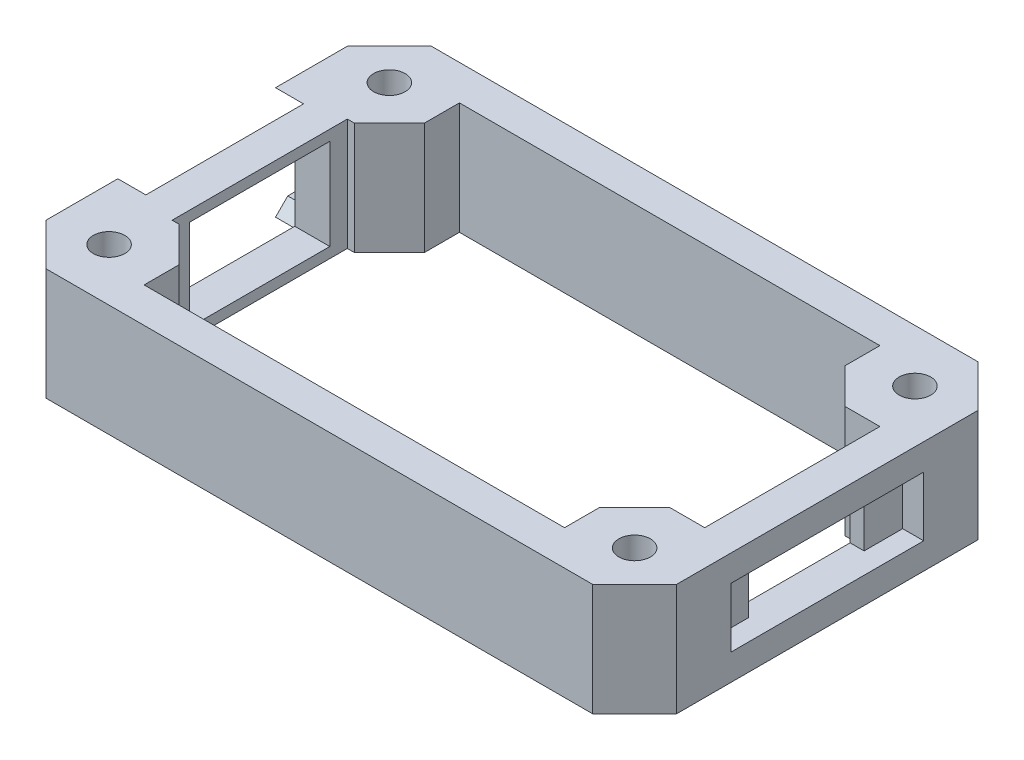
SolidWorks part; units mm, degrees
ref_plane "Front Plane" through (0, 0, 0) normal (0, 0, 1) x (1, 0, 0)
ref_plane "Top Plane" through (0, 0, 0) normal (0, 1, 0) x (1, 0, 0)
ref_plane "Right Plane" through (0, 0, 0) normal (1, 0, 0) x (0, 0, -1)
sketch "Sketch1" plane through (0, 0, 0) normal (0, 1, 0) x (1, 0, 0)
  line L1 (-45, -27.5) -> (45, -27.5)
  line L2 (-45, -27.5) -> (-45, 27.5)
  line L3 (-45, 27.5) -> (45, 27.5)
  line L4 (45, -27.5) -> (45, 27.5)
  line L5 (-45, -27.5) -> (45, 27.5) construction
  line L6 (-45, 27.5) -> (45, -27.5) construction
  point P0 (0, 0)
  dimension "D1" = 55
  dimension "D2" = 90
extrude "Boss-Extrude1" add sketch "Sketch1" along normal blind 16
sketch "Sketch2" plane through (-45, 0, 0) normal (-1, 0, 0) x (0, 0, 1)
  line L0 (-27.5, 0) -> (27.5, 0) construction
  line L1 (-17.5, 1.75) -> (17.5, 1.75)
  line L2 (-17.5, 1.75) -> (-17.5, 14.25)
  line L3 (-17.5, 14.25) -> (17.5, 14.25)
  line L4 (17.5, 1.75) -> (17.5, 14.25)
  line L5 (-17.5, 1.75) -> (17.5, 14.25) construction
  line L6 (-17.5, 14.25) -> (17.5, 1.75) construction
  line L7 (-11, -0.25) -> (11, -0.25)
  line L8 (-11, -0.25) -> (-11, 16.25)
  line L9 (-11, 16.25) -> (11, 16.25)
  line L10 (11, -0.25) -> (11, 16.25)
  line L11 (-11, -0.25) -> (11, 16.25) construction
  line L12 (-11, 16.25) -> (11, -0.25) construction
  line L13 (-27.5, 16) -> (-27.5, 0) construction
  line L14 (-11, 16.25) -> (-13, 14.25)
  line L15 (11, 16.25) -> (13, 14.25)
  line L16 (-11, -0.25) -> (-13, 1.75)
  line L17 (11, -0.25) -> (13, 1.75)
  point P0 (0, 8)
  point P5 (0, 8)
  point P14 (0, 0)
  point P17 (-27.5, 8)
  line M13 (-27.5, 0) -> (27.5, 0)
  line M15 (27.5, 16) -> (-27.5, 16)
  dimension "D1" = 22
  dimension "D2" = 12.5
  dimension "D3" = 35
  dimension "D4" = 16.5
  dimension "D5" = 45
  dimension "D6" = 45
  dimension "D7" = 45
  dimension "D8" = 45
extrude "Cut-Extrude1" cut sketch "Sketch2" against normal blind 4 contours L3 L10 L8 M15 | L15 L10 L3 M15 | L14 L3 L8 M15 | L1 L8 L3 L2 | L1 L10 L3 L8 | L10 L1 L4 L3 | L10 L1 L8 M13 | L17 L1 L10 M13 | L16 L8 L1 M13
sketch "Sketch3" plane through (-41, 0, 0) normal (-1, 0, 0) x (0, 0, 1)
  line L0 (-11, 20.75) -> (11, 20.75) construction
  line L1 (-10, 1.5) -> (10, 1.5)
  line L2 (-10, 1.5) -> (-10, 14.5)
  line L3 (-10, 14.5) -> (10, 14.5)
  line L4 (10, 1.5) -> (10, 14.5)
  line L5 (-10, 1.5) -> (10, 14.5) construction
  line L6 (-10, 14.5) -> (10, 1.5) construction
  line L7 (-17.5, 1.75) -> (-17.5, 14.25) construction
  point P0 (0, 8)
  point P7 (0, 20.75)
  point P11 (-17.5, 8)
  dimension "D1" = 20
  dimension "D2" = 13
extrude "Cut-Extrude2" cut sketch "Sketch3" against normal blind 20
chamfer "Chamfer1" distance 6 angle 45 4 edges at (45, 8, -27.5) (45, 8, 27.5) (-45, 8, 27.5) (-45, 8, -27.5)
hole_wizard "M4 Clearance Hole1" positions "Sketch5" profile "Sketch6" hole size "M4" standard "ANSI Metric" end condition through all
sketch "Sketch5" plane through (0, 16, 0) normal (0, 1, 0) x (1, 0, 0)
  line L2 (-37.5, -20) -> (37.5, -20)
  line L3 (-37.5, -20) -> (-37.5, 20)
  line L4 (-37.5, 20) -> (37.5, 20)
  line L5 (37.5, -20) -> (37.5, 20)
  line L6 (-37.5, -20) -> (37.5, 20) construction
  line L7 (-37.5, 20) -> (37.5, -20) construction
  point P3 (0, 0)
  point P4 (37.5, 20)
  point P105 (-37.5, -20)
  point P106 (-37.5, 20)
  point P107 (37.5, -20)
  dimension "D1" = 75
  dimension "D2" = 40
sketch "Sketch6" plane through (0, 16, 0) normal (1, 0, 0) x (0, 0, 1)
  line L0 (0, 0) -> (0, 16)
  line L1 (0, 16) -> (2.25, 16)
  line L2 (2.25, 16) -> (2.25, 0)
  line L5 (2.25, 0) -> (0, 0)
  line L11 (0, -6.35) -> (0, 107.95) construction
  dimension "Thru Hole Dia." = 4.5
  dimension "Thru Hole Depth" = 16
sketch "Sketch7" plane through (45, 0, 0) normal (1, 0, 0) x (0, 0, -1)
  line L0 (-21.5, 0) -> (21.5, 0) construction
  line L1 (-13.75, 3.75) -> (13.75, 3.75)
  line L2 (-13.75, 3.75) -> (-13.75, 12.25)
  line L3 (-13.75, 12.25) -> (13.75, 12.25)
  line L4 (13.75, 3.75) -> (13.75, 12.25)
  line L5 (-13.75, 3.75) -> (13.75, 12.25) construction
  line L6 (-13.75, 12.25) -> (13.75, 3.75) construction
  line L7 (-21.5, 16) -> (-21.5, 0) construction
  point P0 (0, 8)
  point P5 (0, 0)
  point P8 (0, 0)
  point P11 (-21.5, 8)
  dimension "D1" = 8.5
  dimension "D2" = 27.5
extrude "Cut-Extrude3" cut sketch "Sketch7" against normal blind 3
sketch "Sketch8" plane through (42, 0, 0) normal (1, 0, 0) x (0, 0, -1)
  line L0 (13.75, 12.25) -> (-13.75, 12.25) construction
  line L1 (-8.25, 3.75) -> (8.25, 3.75)
  line L2 (-8.25, 3.75) -> (-8.25, 12.25)
  line L3 (-8.25, 12.25) -> (8.25, 12.25)
  line L4 (8.25, 3.75) -> (8.25, 12.25)
  line L5 (-8.25, 3.75) -> (8.25, 12.25) construction
  line L6 (-8.25, 12.25) -> (8.25, 3.75) construction
  line L7 (-13.75, 3.75) -> (13.75, 3.75) construction
  point P0 (0, 8)
  point P9 (0, 0)
  point P10 (0, 3.75)
  dimension "D1" = 16.5
extrude "Cut-Extrude4" cut sketch "Sketch8" against normal blind 12
sketch "Sketch9" plane through (0, 16, 0) normal (0, 1, 0) x (1, 0, 0)
  line L24 (40, -19.4289) -> (40, 19.4289)
  line L25 (40, 19.4289) -> (36.9289, 22.5)
  line L26 (36.9289, 22.5) -> (-36.9289, 22.5)
  line L27 (-36.9289, 22.5) -> (-40, 19.4289)
  line L28 (-40, 19.4289) -> (-40, 16.25)
  line L29 (-40, 16.25) -> (-36, 16.25)
  line L30 (-36, 16.25) -> (-36, -16.25)
  line L31 (-36, -16.25) -> (-40, -16.25)
  line L32 (-40, -16.25) -> (-40, -19.4289)
  line L33 (-40, -19.4289) -> (-36.9289, -22.5)
  line L34 (-36.9289, -22.5) -> (36.9289, -22.5)
  line L35 (36.9289, -22.5) -> (40, -19.4289)
  line L36 (40, -19.4289) -> (40, 19.4289)
  line L37 (40, 19.4289) -> (36.9289, 22.5)
  line L38 (36.9289, 22.5) -> (-36.9289, 22.5)
  line L39 (-36.9289, 22.5) -> (-40, 19.4289)
  line L40 (-40, 19.4289) -> (-40, 16.25)
  line L41 (-40, 16.25) -> (-36, 16.25)
  line L42 (-36, 16.25) -> (-36, -16.25)
  line L43 (-36, -16.25) -> (-40, -16.25)
  line L44 (-40, -16.25) -> (-40, -19.4289)
  line L45 (-40, -19.4289) -> (-36.9289, -22.5)
  line L46 (-36.9289, -22.5) -> (36.9289, -22.5)
  line L47 (36.9289, -22.5) -> (40, -19.4289)
  line L79 (30, -12.5) -> (40, -12.5)
  line L80 (30, -12.5) -> (30, -22.5)
  line L81 (30, -22.5) -> (40, -22.5)
  line L82 (40, -12.5) -> (40, -22.5)
  line L83 (-30, -12.5) -> (-40, -12.5)
  line L84 (-30, -12.5) -> (-30, -22.5)
  line L85 (-30, -22.5) -> (-40, -22.5)
  line L86 (-40, -12.5) -> (-40, -22.5)
  line L87 (-30, 12.5) -> (-40, 12.5)
  line L88 (-30, 12.5) -> (-30, 22.5)
  line L89 (-30, 22.5) -> (-40, 22.5)
  line L90 (-40, 12.5) -> (-40, 22.5)
  line L91 (30, 12.5) -> (40, 12.5)
  line L92 (30, 12.5) -> (30, 22.5)
  line L93 (30, 22.5) -> (40, 22.5)
  line L94 (40, 12.5) -> (40, 22.5)
  circle M29 centre (0, 0) radius 2.25
  dimension "D2" = 10
  dimension "D1" = 5
extrude "Cut-Extrude5" cut sketch "Sketch9" against normal through all contours L91 L92 L38 L88 L87 L42 L83 L84 L46 L80 L79 L36 M29
chamfer "Chamfer2" distance 5 angle 45 4 edges at (-30, 8, -12.5) (-30, 8, 12.5) (30, 8, -12.5) (30, 8, 12.5)
